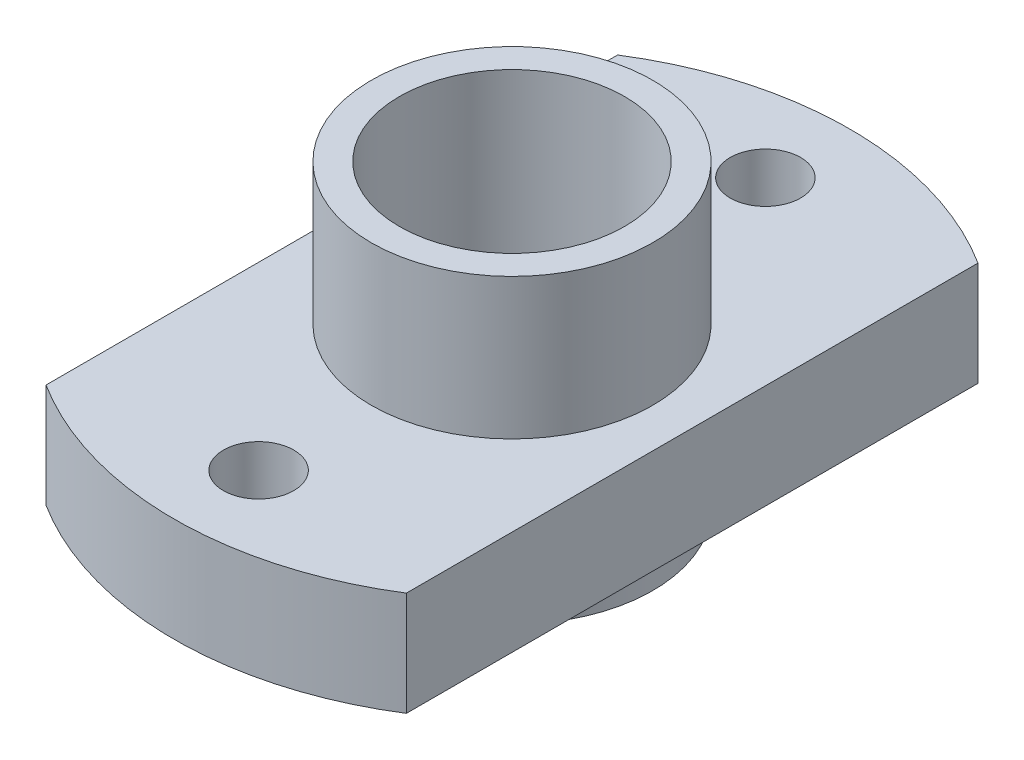
SolidWorks part; units mm, degrees
ref_plane "Front Plane" through (0, 0, 0) normal (0, 0, 1) x (1, 0, 0)
ref_plane "Top Plane" through (0, 0, 0) normal (0, 1, 0) x (1, 0, 0)
ref_plane "Right Plane" through (0, 0, 0) normal (1, 0, 0) x (0, 0, -1)
sketch "Sketch1" plane through (0, 0, 0) normal (0, 1, 0) x (1, 0, 0)
  line L0 (0, 0) -> (0, 50000) construction
  line L1 (-6.4, 10.1509) -> (-6.4, -10.1509)
  line L2 (6.4, 10.1509) -> (6.4, -10.1509)
  arc A0 (-6.4, -10.1509) -> (6.4, -10.1509) centre (0, 0) ccw
  arc A1 (6.4, 10.1509) -> (-6.4, 10.1509) centre (0, 0) ccw
  dimension "D1" = 24
  dimension "D2" = 12.8
extrude "Boss-Extrude1" add sketch "Sketch1" along normal blind 3.7
sketch "Sketch2" plane through (0, 3.7, 0) normal (0, 1, 0) x (1, 0, 0)
  circle A0 centre (0, 0) radius 5
  dimension "D1" = 10
extrude "Boss-Extrude2" add sketch "Sketch2" along normal blind 5 and the other way blind 5.7
hole_wizard "M3 螺纹孔1" positions "草图1" profile "草图2" tap size "M3" standard "GB" end condition up to next
sketch "草图1" plane through (0, 0, 0) normal (0, -1, 0) x (-1, 0, 0)
  line L0 (-11.7727, 0) -> (15.57, 0) construction
  point P0 (0, -9)
  point P2 (0, 9)
  dimension "D1" = 18
sketch "草图2" plane through (0, 0, 9) normal (1, 0, 0) x (0, 0, -1)
  line L0 (0, 0) -> (0, 3.7)
  line L1 (0, 3.7) -> (1.25, 3.7)
  line L2 (1.25, 3.7) -> (1.25, 0)
  line L5 (1.25, 0) -> (0, 0)
  line L11 (0, -6.35) -> (0, 107.95) construction
  dimension "通孔螺纹孔钻头直径" = 2.5
  dimension "通孔螺纹孔钻头深度" = 3.7
cosmetic thread "孔螺蚊线1" parameters "D2"=3
cosmetic thread "孔螺蚊线2" parameters "D2"=3
sketch "草图3" plane through (0, -2, 0) normal (0, -1, 0) x (1, 0, 0)
  circle A0 centre (0, 0) radius 4
  dimension "D1" = 8
extrude "切除-拉伸1" cut sketch "草图3" against normal up to next
